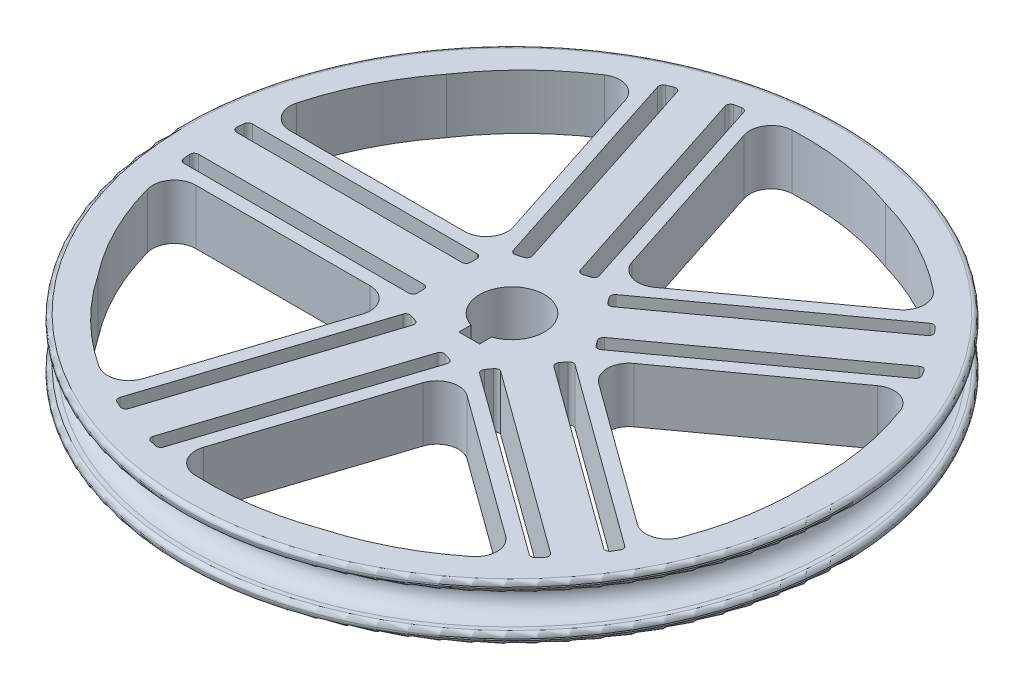
SolidWorks part; units mm, degrees
material "6061 Alloy"
ref_plane "Front Plane" through (0, 0, 0) normal (0, 0, 1) x (1, 0, 0)
ref_plane "Top Plane" through (0, 0, 0) normal (0, 1, 0) x (1, 0, 0)
ref_plane "Right Plane" through (0, 0, 0) normal (1, 0, 0) x (0, 0, -1)
sketch "Sketch1" plane through (0, 0, 0) normal (0, 0, 1) x (1, 0, 0)
  line L3 (0, 8) -> (-1, 8)
  line L4 (0, 0) -> (-1, 0)
  line L5 (-2, 9) -> (-2, 9.35)
  line L6 (-1, 10.35) -> (74.2, 10.35)
  line L7 (0, 4) -> (7.1457, 4) construction
  line L8 (-2, -1) -> (-2, -1.35)
  line L9 (-1, -2.35) -> (74.2, -2.35)
  line L10 (74.2, 10.35) -> (74.2, -2.35)
  arc A1 (0, 8) -> (0, 0) centre (0, 4) cw
  arc A2 (-1, 8) -> (-2, 9) centre (-1, 9) cw
  arc A3 (-1, 0) -> (-2, -1) centre (-1, -1) ccw
  arc A4 (-2, 9.35) -> (-1, 10.35) centre (-1, 9.35) cw
  arc A5 (-2, -1.35) -> (-1, -2.35) centre (-1, -1.35) ccw
  point P14 (-2, 8)
  point P17 (-2, 0)
  point P20 (-2, 10.35)
  point P23 (-2, -2.35)
  dimension "D2" = 4
  dimension "D7" = 1
  dimension "D8" = 1
  dimension "D1" = 8
  dimension "D3" = 2
  dimension "D4" = 2
  dimension "D5" = 76.2
  dimension "D6" = 2.35
revolve "Revolve2" add sketch "Sketch1" angle 360 about L10
sketch "Sketch2" plane through (0, -2.35, 0) normal (0, -1, 0) x (1, 0, 0)
  line L5 (71.2, 0) -> (128.6984, 0) construction
  circle A0 centre (74.2, 0) radius 7.5
  dimension "D1" = 15
extrude "Cut-Extrude3" cut sketch "Sketch2" against normal through all
sketch "Sketch3" plane through (0, -2.35, 0) normal (0, -1, 0) x (1, 0, 0)
  line L0 (71.2, 0) -> (130.5671, 0) construction
  line L2 (92.741, 0) -> (79.9295, 17.6336)
  line L3 (79.9295, 17.6336) -> (59.2, 10.8981)
  line L4 (59.2, 10.8981) -> (59.2, -10.8981)
  line L5 (59.2, -10.8981) -> (79.9295, -17.6336)
  line L6 (79.9295, -17.6336) -> (92.741, 0)
  line L7 (74.2, 0) -> (79.9295, 17.6336)
  line L8 (79.9295, 17.6336) -> (95.3803, 65.1864)
  line L9 (74.2, 0) -> (92.741, 0)
  line L10 (92.741, 0) -> (142.741, 0)
  line L11 (83.7501, 12.3749) -> (127.5759, 44.2162)
  line L12 (88.9204, 5.2586) -> (132.7462, 37.0999)
  line L13 (79.9295, 17.6336) -> (123.1357, 49.0247)
  line L14 (81.6928, 15.2065) -> (125.2514, 46.8536)
  line L15 (92.741, 0) -> (135.9473, 31.3912)
  line L16 (90.9777, 2.4271) -> (134.5362, 34.0742)
  circle A1 centre (74.2, 0) radius 15 construction
  arc A2 (95.3803, 65.1864) -> (142.741, 0) centre (77.3306, 2.2745) cw
  dimension "D5" = 90
  dimension "D6" = 90
  dimension "D7" = 6.5
  dimension "D1" = 30
  dimension "D4" = 65.45
  dimension "D2" = 50
  dimension "D3" = 50
  dimension "D8" = 6.5
  dimension "D9" = 3
  dimension "D10" = 90
  dimension "D11" = 3
sketch "Sketch5" plane through (0, -2.35, 0) normal (0, -1, 0) x (1, 0, 0)
  line L0 (74.2, 0) -> (74.2, 9.89)
  line L1 (71.81, 9.89) -> (76.59, 9.89)
  line L4 (74.2, 9.89) -> (74.2, 7.5)
  line L5 (71.81, 9.89) -> (71.81, 6.6936)
  line L6 (76.59, 9.89) -> (76.59, 6.6936)
  line L7 (71.81, 6.6936) -> (76.59, 6.6936)
  circle A1 centre (74.2, 0) radius 7.5 construction
  dimension "D2" = 2.39
  dimension "D1" = 2.39
extrude "Cut-Extrude5" cut sketch "Sketch5" against normal through all
extrude "Cut-Extrude7" cut sketch "Sketch3" against normal through all both and the other way through all contours A2 L8 L13 | A2 L14 L2 L11 | A2 L12 L2 L16 | A2 L15 L10
pattern_circular "CirPattern1" count 5 over 360 about axis through (74.2, 0, 0) along (0, 1, 0) of "Cut-Extrude7"
fillet "Fillet1" radius 5 5 edges at (79.9295, 4, -17.6336) (92.741, 4, 0) (79.9295, 4, 17.6336) (59.2, 4, 10.8981) (59.2, 4, -10.8981)
fillet "Fillet2" radius 5 10 edges at (123.1357, 4, 49.0247) (135.9473, 4, 31.3912) (135.9473, 4, -31.3912) (123.1357, 4, -49.0247) (42.6967, 4, -61.6901) (63.4262, 4, -68.4256) (5.7941, 4, -10.8981) (5.7941, 4, 10.8981) (42.6967, 4, 61.6901) (63.4262, 4, 68.4256)
fillet "Fillet3" radius 1 40 edges at (134.5362, 4, -34.0742) (127.5759, 4, -44.2162) (125.2514, 4, -46.8536) (132.7462, 4, -37.0999) (60.4385, 4, -67.9126) (48.6419, 4, -64.427) (57.0077, 4, -67.1452) (45.4153, 4, -63.0313) (5.0284, 4, 4.3981) (5.3587, 4, -7.8981) (5.0284, 4, -4.3981) (5.3587, 4, 7.8981) (60.4385, 4, 67.9126) (48.6419, 4, 64.427) (45.4153, 4, 63.0313) (57.0077, 4, 67.1452) (62.0532, 4, 11.8252) (73.7476, 4, 15.6249) (77.0763, 4, 16.7065) (65.3819, 4, 12.9067) (59.2, 4, 4.3981) (59.2, 4, -7.8981) (59.2, 4, 7.8981) (59.2, 4, -4.3981) (77.0763, 4, -16.7065) (65.3819, 4, -12.9067) (62.0532, 4, -11.8252) (73.7476, 4, -15.6249) (83.7501, 4, -12.3749) (90.9777, 4, -2.4271) (81.6928, 4, -15.2065) (88.9204, 4, -5.2586) (88.9204, 4, 5.2586) (90.9777, 4, 2.4271) (134.5362, 4, 34.0742) (132.7462, 4, 37.0999) (125.2514, 4, 46.8536) (127.5759, 4, 44.2162) (83.7501, 4, 12.3749) (81.6928, 4, 15.2065)
sketch "Sketch6" plane through (0, -2.35, 0) normal (0, -1, 0) x (1, 0, 0)
  line L1 (76.9785, 36.1222) -> (102.3785, 36.1222)
  line L2 (76.9785, 36.1222) -> (76.9785, 61.5222)
  line L3 (76.9785, 61.5222) -> (102.3785, 61.5222)
  line L4 (102.3785, 36.1222) -> (102.3785, 61.5222)
  dimension "D1" = 25.4
  dimension "D2" = 25.4
